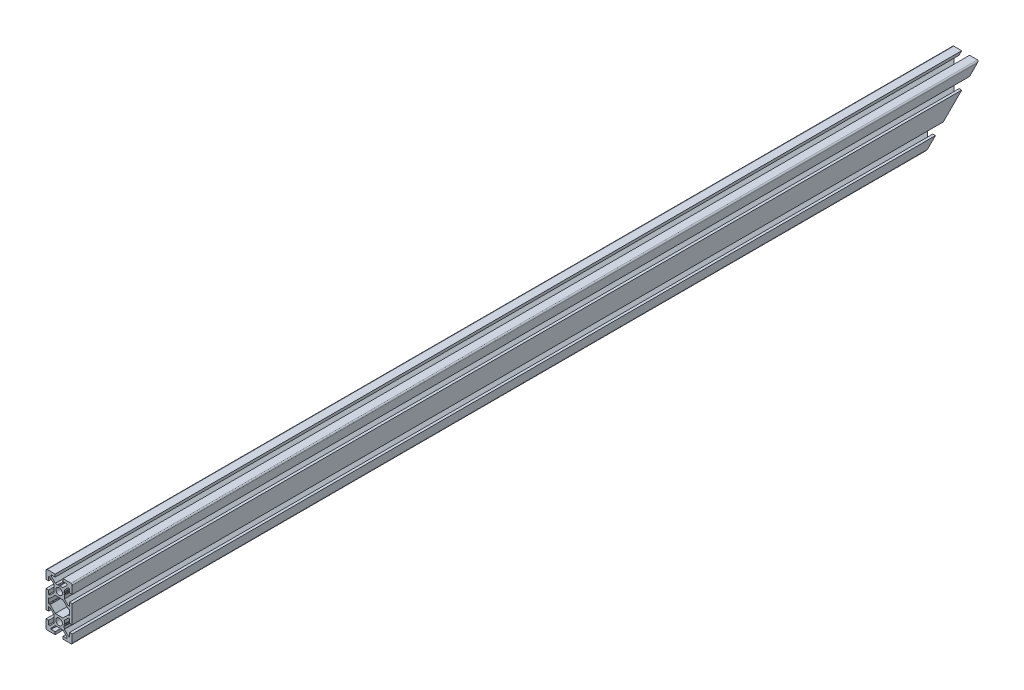
SolidWorks part; units mm, degrees
material "6063-T1"
ref_plane "Front Plane" through (0, 0, 0) normal (0, 0, 1) x (1, 0, 0)
ref_plane "Top Plane" through (0, 0, 0) normal (0, 1, 0) x (1, 0, 0)
ref_plane "Right Plane" through (0, 0, 0) normal (1, 0, 0) x (0, 0, -1)
ref_plane "Plane1" through (0, 0, -600) normal (0, 0, -1) x (-1, 0, 0)
sketch "Sketch1" plane through (0, 0, -600) normal (0, 0, -1) x (-1, 0, 0)
  line L0 (8, 1.7) -> (8, -1.7)
  line L1 (7.7, -2) -> (7.0636, -2)
  line L2 (6.8515, -2.0879) -> (2.9393, -6)
  line L3 (2.9393, -6) -> (-2.9393, -6)
  line L4 (-2.9393, -6) -> (-6.8515, -2.0879)
  line L5 (-7.0636, -2) -> (-7.7, -2)
  line L6 (-8, -1.7) -> (-8, 1.7)
  line L7 (-7.7, 2) -> (-7.0636, 2)
  line L8 (-6.8515, 2.0879) -> (-2.9393, 6)
  line L9 (-2.9393, 6) -> (2.9393, 6)
  line L10 (2.9393, 6) -> (6.8515, 2.0879)
  line L11 (7.0636, 2) -> (7.7, 2)
  line L12 (10, -7) -> (10, 7)
  line L13 (10, 7) -> (8, 7)
  line L14 (8, 7) -> (8, 4)
  line L15 (8, 4) -> (7.0607, 4)
  line L16 (7.0607, 4) -> (4, 7.0607)
  line L17 (4, 7.0607) -> (4, 7.5)
  line L18 (4, 7.5) -> (3.751, 8.7811)
  line L19 (3.751, 8.7811) -> (3.933, 9.0964)
  line L20 (3.933, 9.5964) -> (3.7, 10)
  line L21 (3.7, 10) -> (3.933, 10.4036)
  line L22 (4, 10.6536) -> (4, 12.9393)
  line L23 (4, 12.9393) -> (7.0607, 16)
  line L24 (7.0607, 16) -> (8, 16)
  line L25 (8, 16) -> (8, 13)
  line L26 (8, 13) -> (10, 13)
  line L27 (10, 13) -> (10, 19)
  line L28 (9, 20) -> (3, 20)
  line L29 (3, 20) -> (3, 18)
  line L30 (3, 18) -> (6, 18)
  line L31 (6, 18) -> (6, 17.0607)
  line L32 (6, 17.0607) -> (2.9393, 14)
  line L33 (2.9393, 14) -> (2.5, 14)
  line L34 (2.5, 14) -> (1.2189, 13.751)
  line L35 (1.2189, 13.751) -> (0.9036, 13.933)
  line L36 (0.4036, 13.933) -> (0, 13.7)
  line L37 (0, 13.7) -> (-0.4036, 13.933)
  line L38 (-0.6536, 14) -> (-2.9393, 14)
  line L39 (-2.9393, 14) -> (-6, 17.0607)
  line L40 (-6, 17.0607) -> (-6, 18)
  line L41 (-6, 18) -> (-3, 18)
  line L42 (-3, 18) -> (-3, 20)
  line L43 (-3, 20) -> (-9, 20)
  line L44 (-10, 19) -> (-10, 13)
  line L45 (-10, 13) -> (-8, 13)
  line L46 (-8, 13) -> (-8, 16)
  line L47 (-8, 16) -> (-7.0607, 16)
  line L48 (-7.0607, 16) -> (-4, 12.9393)
  line L49 (-4, 12.9393) -> (-4, 12.5)
  line L50 (-4, 12.5) -> (-3.751, 11.2189)
  line L51 (-3.751, 11.2189) -> (-3.933, 10.9036)
  line L52 (-3.933, 10.4036) -> (-3.7, 10)
  line L53 (-3.7, 10) -> (-3.933, 9.5964)
  line L54 (-4, 9.3464) -> (-4, 7.0607)
  line L55 (-4, 7.0607) -> (-7.0607, 4)
  line L56 (-7.0607, 4) -> (-8, 4)
  line L57 (-8, 4) -> (-8, 7)
  line L58 (-8, 7) -> (-10, 7)
  line L59 (-10, 7) -> (-10, -7)
  line L60 (-10, -7) -> (-8, -7)
  line L61 (-8, -7) -> (-8, -4)
  line L62 (-8, -4) -> (-7.0607, -4)
  line L63 (-7.0607, -4) -> (-4, -7.0607)
  line L64 (-4, -7.0607) -> (-4, -9.3464)
  line L65 (-3.933, -9.5964) -> (-3.7, -10)
  line L66 (-3.7, -10) -> (-3.933, -10.4036)
  line L67 (-3.933, -10.9036) -> (-3.751, -11.2189)
  line L68 (-3.751, -11.2189) -> (-4, -12.5)
  line L69 (-4, -12.5) -> (-4, -12.9393)
  line L70 (-4, -12.9393) -> (-7.0607, -16)
  line L71 (-7.0607, -16) -> (-8, -16)
  line L72 (-8, -16) -> (-8, -13)
  line L73 (-8, -13) -> (-10, -13)
  line L74 (-10, -13) -> (-10, -19)
  line L75 (-9, -20) -> (-3, -20)
  line L76 (-3, -20) -> (-3, -18)
  line L77 (-3, -18) -> (-6, -18)
  line L78 (-6, -18) -> (-6, -17.0607)
  line L79 (-6, -17.0607) -> (-2.9393, -14)
  line L80 (-2.9393, -14) -> (-0.6536, -14)
  line L81 (-0.4036, -13.933) -> (0, -13.7)
  line L82 (0, -13.7) -> (0.4036, -13.933)
  line L83 (0.9036, -13.933) -> (1.2189, -13.751)
  line L84 (1.2189, -13.751) -> (2.5, -14)
  line L85 (2.5, -14) -> (2.9393, -14)
  line L86 (2.9393, -14) -> (6, -17.0607)
  line L87 (6, -17.0607) -> (6, -18)
  line L88 (6, -18) -> (3, -18)
  line L89 (3, -18) -> (3, -20)
  line L90 (3, -20) -> (9, -20)
  line L91 (10, -19) -> (10, -13)
  line L92 (10, -13) -> (8, -13)
  line L93 (8, -13) -> (8, -16)
  line L94 (8, -16) -> (7.0607, -16)
  line L95 (7.0607, -16) -> (4, -12.9393)
  line L96 (4, -12.9393) -> (4, -10.6536)
  line L97 (3.933, -10.4036) -> (3.7, -10)
  line L98 (3.7, -10) -> (3.933, -9.5964)
  line L99 (3.933, -9.0964) -> (3.751, -8.7811)
  line L100 (3.751, -8.7811) -> (4, -7.5)
  line L101 (4, -7.5) -> (4, -7.0607)
  line L102 (4, -7.0607) -> (7.0607, -4)
  line L103 (7.0607, -4) -> (8, -4)
  line L104 (8, -4) -> (8, -7)
  line L105 (8, -7) -> (10, -7)
  circle A0 centre (0, -10) radius 2.5
  circle A1 centre (0, 10) radius 2.5
  arc A2 (7.7, 2) -> (8, 1.7) centre (7.7, 1.7) cw
  arc A3 (8, -1.7) -> (7.7, -2) centre (7.7, -1.7) cw
  arc A4 (7.0636, -2) -> (6.8515, -2.0879) centre (7.0636, -2.3) ccw
  arc A5 (-6.8515, -2.0879) -> (-7.0636, -2) centre (-7.0636, -2.3) ccw
  arc A6 (-7.7, -2) -> (-8, -1.7) centre (-7.7, -1.7) cw
  arc A7 (-8, 1.7) -> (-7.7, 2) centre (-7.7, 1.7) cw
  arc A8 (-7.0636, 2) -> (-6.8515, 2.0879) centre (-7.0636, 2.3) ccw
  arc A9 (6.8515, 2.0879) -> (7.0636, 2) centre (7.0636, 2.3) ccw
  arc A10 (3.933, 9.0964) -> (3.933, 9.5964) centre (3.5, 9.3464) ccw
  arc A11 (3.933, 10.4036) -> (4, 10.6536) centre (3.5, 10.6536) ccw
  arc A12 (10, 19) -> (9, 20) centre (9, 19) ccw
  arc A13 (0.9036, 13.933) -> (0.4036, 13.933) centre (0.6536, 13.5) ccw
  arc A14 (-0.4036, 13.933) -> (-0.6536, 14) centre (-0.6536, 13.5) ccw
  arc A15 (-9, 20) -> (-10, 19) centre (-9, 19) ccw
  arc A16 (-3.933, 10.9036) -> (-3.933, 10.4036) centre (-3.5, 10.6536) ccw
  arc A17 (-3.933, 9.5964) -> (-4, 9.3464) centre (-3.5, 9.3464) ccw
  arc A18 (-4, -9.3464) -> (-3.933, -9.5964) centre (-3.5, -9.3464) ccw
  arc A19 (-3.933, -10.4036) -> (-3.933, -10.9036) centre (-3.5, -10.6536) ccw
  arc A20 (-10, -19) -> (-9, -20) centre (-9, -19) ccw
  arc A21 (-0.6536, -14) -> (-0.4036, -13.933) centre (-0.6536, -13.5) ccw
  arc A22 (0.4036, -13.933) -> (0.9036, -13.933) centre (0.6536, -13.5) ccw
  arc A23 (9, -20) -> (10, -19) centre (9, -19) ccw
  arc A24 (4, -10.6536) -> (3.933, -10.4036) centre (3.5, -10.6536) ccw
  arc A25 (3.933, -9.5964) -> (3.933, -9.0964) centre (3.5, -9.3464) ccw
  dimension "D1" = 5
  dimension "D3" = 0.3
  dimension "D4" = 0.3
  dimension "D5" = 0.3
  dimension "D6" = 0.3
  dimension "D7" = 0.3
  dimension "D8" = 0.3
  dimension "D9" = 0.3
  dimension "D10" = 0.5
  dimension "D11" = 0.5
  dimension "D12" = 1
  dimension "D13" = 0.5
  dimension "D14" = 0.5
  dimension "D15" = 1
  dimension "D16" = 0.5
  dimension "D17" = 0.5
  dimension "D18" = 0.5
  dimension "D19" = 0.5
  dimension "D20" = 0.4036
  dimension "D21" = 0.5
  dimension "D22" = 0.5
  dimension "D23" = 1
  dimension "D24" = 0.5
  dimension "D25" = 0.5
  dimension "D26" = 0.4036
  dimension "D27" = 0.6536
  dimension "D28" = 0.6536
  dimension "D29" = 0.9036
  dimension "D30" = 0.9036
  dimension "D31" = 1.2189
  dimension "D32" = 1.2189
  dimension "D33" = 2.5
  dimension "D34" = 2.5
  dimension "D35" = 2.9393
  dimension "D36" = 2.9393
  dimension "D37" = 3
  dimension "D38" = 3.5
  dimension "D39" = 6
  dimension "D40" = 6.8515
  dimension "D41" = 3.7
  dimension "D42" = 3.7
  dimension "D43" = 3.751
  dimension "D44" = 3.751
  dimension "D45" = 3.933
  dimension "D46" = 3.933
  dimension "D47" = 6.8515
  dimension "D48" = 7.0607
  dimension "D49" = 7.0607
  dimension "D50" = 7.0636
  dimension "D51" = 7.0636
  dimension "D52" = 8
  dimension "D53" = 10
  dimension "D54" = 3
  dimension "D55" = 4
  dimension "D56" = 6
  dimension "D57" = 6.8515
  dimension "D58" = 6.8515
  dimension "D59" = 7.0607
  dimension "D60" = 7.0607
  dimension "D61" = 0.4036
  dimension "D62" = 0.4036
  dimension "D63" = 0.6536
  dimension "D64" = 0.6536
  dimension "D65" = 2.9393
  dimension "D66" = 2.9393
  dimension "D67" = 8
  dimension "D68" = 2
  dimension "D69" = 3.5
  dimension "D70" = 3.5
  dimension "D71" = 3.7
  dimension "D72" = 3.7
  dimension "D73" = 3.751
  dimension "D74" = 3.751
  dimension "D75" = 3.933
  dimension "D76" = 3.933
  dimension "D77" = 4
  dimension "D78" = 6
  dimension "D79" = 7
  dimension "D80" = 7.0607
  dimension "D81" = 7.0607
  dimension "D82" = 7.5
  dimension "D83" = 8.7811
  dimension "D84" = 9.0964
  dimension "D85" = 9.3464
  dimension "D86" = 9.3464
  dimension "D87" = 9.5964
  dimension "D88" = 9.5964
  dimension "D89" = 10.4036
  dimension "D90" = 12.5
  dimension "D91" = 13
  dimension "D92" = 13.5
  dimension "D93" = 13.5
  dimension "D94" = 18
  dimension "D95" = 20
  dimension "D96" = 2
  dimension "D97" = 4
  dimension "D98" = 6
  dimension "D99" = 7
  dimension "D100" = 7.0607
  dimension "D101" = 7.0607
  dimension "D102" = 7.5
  dimension "D103" = 8.7811
  dimension "D104" = 9.0964
  dimension "D105" = 9.3464
  dimension "D106" = 9.3464
  dimension "D107" = 9.5964
  dimension "D108" = 9.5964
  dimension "D109" = 10.4036
  dimension "D110" = 12.5
  dimension "D111" = 13
  dimension "D112" = 18
extrude "Boss-Extrude1" add sketch "Sketch1" against normal mid plane 691
sketch "Sketch2" [suppressed] plane through (-10, 0, 0) normal (-1, 0, 0) x (0, 0, 1)
  line L0 (-705.695, 20) -> (-665.695, -20)
  line L1 (-494.305, -20) -> (-705.695, -20) construction
  line L2 (-705.695, -7) -> (-705.695, 7) construction
  line L3 (-705.695, 20) -> (-705.695, -20)
  line L4 (-705.695, -20) -> (-665.695, -20)
  dimension "D1" = 45
extrude "Cut-Extrude1" [suppressed] cut sketch "Sketch2" against normal through all
sketch "Sketch3" plane through (-10, 0, 0) normal (-1, 0, 0) x (0, 0, 1)
  line L0 (-945.5, 20) -> (-905.5, -20)
  line L1 (-254.5, -20) -> (-945.5, -20) construction
  line L2 (-905.5, -20) -> (-945.5, -20)
  line L3 (-945.5, -20) -> (-945.5, 20)
  dimension "D1" = 45
extrude "Cut-Extrude2" cut sketch "Sketch3" against normal through all
sketch "Sketch4" plane through (-10, 0, 0) normal (-1, 0, 0) x (0, 0, 1)
  line L0 (-264.5, 20) -> (-264.5, 0) construction
  line L4 (-254.5, 20) -> (-945.5, 20) construction
  line L5 (-264.5, 0) -> (-264.5, -20) construction
  line L6 (-254.5, -20) -> (-905.5, -20) construction
  line L7 (-254.5, -7) -> (-254.5, 7) construction
  circle A0 centre (-264.5, 10) radius 2
  circle A1 centre (-264.5, -10) radius 2
  dimension "D3" = 4
  dimension "D4" = 4
  dimension "D1" = 10
  dimension "D2" = 20
extrude "Cut-Extrude3" cut sketch "Sketch4" against normal through all
